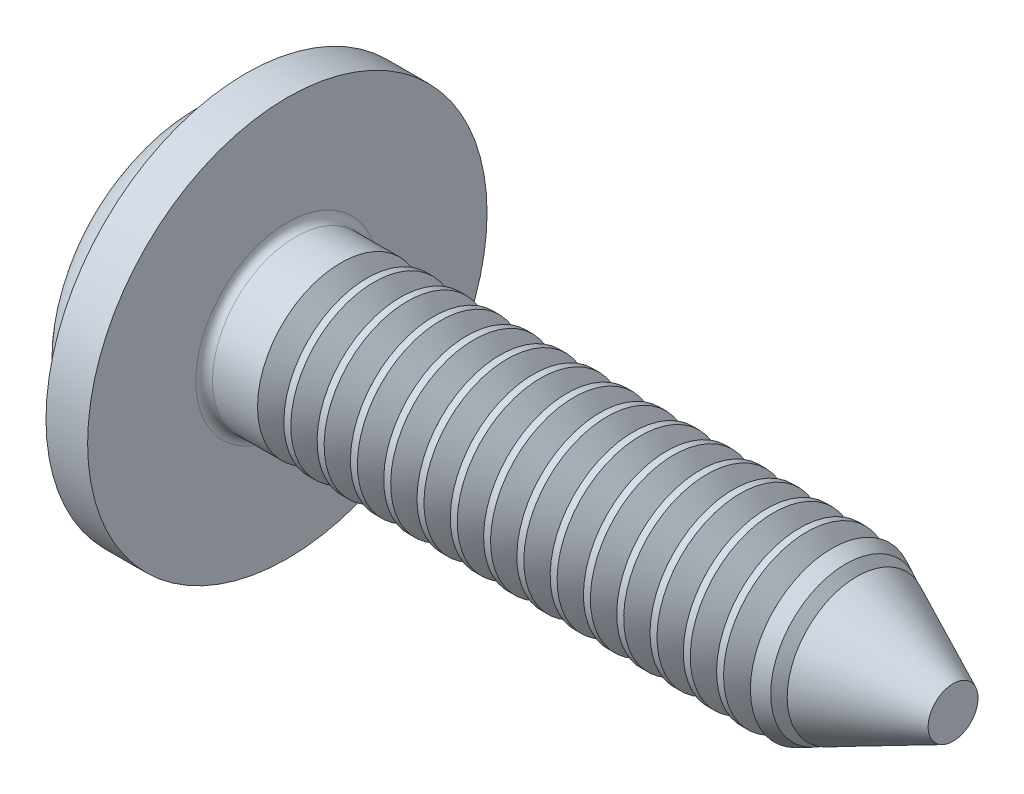
SolidWorks part; units mm, degrees
material "Aço NB 1045"
ref_plane "Plane1" through (0, 0, 0) normal (0, 0, 1) x (1, 0, 0)
ref_plane "Plane2" through (0, 0, 0) normal (0, 1, 0) x (1, 0, 0)
ref_plane "Plane3" through (0, 0, 0) normal (1, 0, 0) x (0, 0, -1)
sketch "BodySke" plane through (0, 0, 0) normal (0, 0, 1) x (1, 0, 0)
  line L0 (1.6, 1) -> (1.6, 2)
  line L1 (1.8, 6.35) -> (1.8, -3.175) construction
  line L2 (-25.4, 0) -> (127, 0) construction
  line L3 (9.6, 0) -> (0, 0)
  line L4 (1.6, 1) -> (9.6, 1)
  line L5 (9.6, 1) -> (9.6, 0)
  line L6 (1.1, 2) -> (1.6, 2)
  line L8 (1.6, 6.35) -> (1.6, -3.175) construction
  arc A0 (0.3941, 1.5765) -> (0, 0) centre (3.35, 0) ccw
  arc A2 (0.3941, 1.5765) -> (1.1, 2) centre (1.1, 1.2) cw
  dimension "D2" = 0.8
  dimension "Length" = 8
  dimension "Head_ht" = 1.6
  dimension "Head_dia" = 4
  dimension "Advance" = 0.4
  dimension "Thread_nom" = 8
  dimension "Diameter" = 2
  dimension "D1" = 0.5
revolve "Base-Revolve" add sketch "BodySke"
cosmetic thread "ThreadCosmetic" [suppressed]
fillet "Fillet1" radius 0.1 1 edges at (1.6, 0, 1)
sketch "Sketch3" plane through (0, 0, 0) normal (1, 0, 0) x (0, 0, -1)
  line L0 (0.24, -1.05) -> (-0.24, -1.05)
  line L1 (0.24, -1.05) -> (0.24, 1.05)
  line L2 (-0.24, 1.05) -> (0.24, 1.05)
  line L3 (-0.24, 1.05) -> (-0.24, -1.05)
  dimension "Cross_dia" = 2.1
  dimension "D1" = 1.05
  dimension "Cross_width" = 0.48
  dimension "D2" = 0.24
ref_plane "Plane4" through (1.42, 0, 0) normal (1, 0, 0) x (0, 0, -1)
sketch "Sketch4" plane through (1.42, 0, 0) normal (1, 0, 0) x (0, 0, -1)
  line L0 (0.24, -0.342) -> (-0.24, -0.342)
  line L1 (0.24, -0.342) -> (0.24, 0.342)
  line L2 (-0.24, 0.342) -> (0.24, 0.342)
  line L3 (-0.24, 0.342) -> (-0.24, -0.342)
  dimension "D1" = 0.48
  dimension "D2" = 0.684
  dimension "D3" = 0.24
  dimension "D4" = 0.342
loft "Recess" cut profiles "Sketch3", "Sketch4"
pattern_circular "RecPat" count 2 every 90 about axis through (0, 0, 0) along (1, 0, 0) of "Recess"
sketch "RecCorSke" plane through (0, 0, 0) normal (0, 0, 1) x (1, 0, 0)
  line L0 (-3.175, 0) -> (15.875, 0) construction
  line L1 (-25.4, 0) -> (127, 0) construction
  line L2 (0, 0) -> (0, 0.4548)
  line L3 (0, 0.4548) -> (1.42, 0.3555)
  line L4 (1.42, 0.3555) -> (1.5355, 0)
  line L5 (1.5355, 0) -> (0, 0)
  dimension "Diameter" = 0.711
  dimension "Depth" = 1.42
  dimension "Draft_angle" = 4
  dimension "Bottom_angle" = 18
revolve "RecessCore" cut sketch "RecCorSke" angle 360 about L0
sketch "ThdSchSke" plane through (0, 0, 0) normal (0, 0, 1) x (1, 0, 0)
  line L0 (2.4, -0.774) -> (2.2418, -1)
  line L1 (2.4, -0.774) -> (2.5582, -1)
  line L2 (2.5582, -1) -> (2.5582, -1.25)
  line L3 (-3.175, 0) -> (5.1513, 0) construction
  line L5 (2.5582, -1.25) -> (2.2418, -1.25)
  line L6 (2.2418, -1.25) -> (2.2418, -1)
  dimension "Diameter" = 2
  dimension "SideAngle" = 55
  dimension "VeeAngle" = 70
  dimension "Thread_minor" = 1.548
  dimension "Overcut" = 2.5
  dimension "Start" = 2.4
revolve "ThreadSchematic" cut sketch "ThdSchSke" angle 360 about L3
pattern_linear "ThdSchPat" count 19 spacing 0.4 along (1, 0, 0) of "ThreadSchematic"
sketch "Esboço1" plane through (1.6, 0, 0) normal (1, 0, 0) x (0, 0, -1)
  circle A0 centre (0, 0) radius 2.4
  dimension "D1" = 4.8
extrude "Ressalto-extrusão1" add sketch "Esboço1" against normal blind 0.5
sketch "Esboço2" plane through (0, 0, 0) normal (0, 1, 0) x (1, 0, 0)
  line L0 (0, 0) -> (9.6, 0) construction
  line L1 (9.6, -0.774) -> (9.6, 0.774) construction
  line L2 (9.6, 0.3) -> (8.1, 1)
  line L4 (8.1, 1) -> (9.6, 1)
  line L5 (9.6, 1) -> (9.6, 0.3)
  line L6 (7.4418, 1) -> (7.3582, 1) construction
  dimension "D1" = 1.5
  dimension "D2" = 0.6
revolve "Corte-Revolução1" cut sketch "Esboço2" angle 360 about L0
equation "\"D1@Sketch3\" = \"Cross_dia@Sketch3\" / 2"
equation "\"D2@Sketch3\" = \"Cross_width@Sketch3\" / 2"
equation "\"Depth@RecCorSke\" = \"Cross_depth@Plane4\""
equation "\"D1@Sketch4\" = \"Cross_width@Sketch3\""
equation "\"D2@Sketch4\" = \"Cross_dia@Sketch3\" - 2.0 * \"Cross_depth@Plane4\" * tan(26.5  * 0.017453292)"
equation "\"D3@Sketch4\" = \"D1@Sketch4\" / 2"
equation "\"D4@Sketch4\" = \"D2@Sketch4\" / 2"
equation "\"Thread_length@ThreadCosmetic\" = ((sgn( (\"Length@BodySke\" - \"Advance@BodySke\" * 2.0 ) - \"Thread_nom@BodySke\" )-1)*( (\"Length@BodySke\" - \"Advance@BodySke\" * 2.0 ) - \"Thread_nom@BodySke\" ))/-2+ \"Thread_nom@BodySke\""
equation "\"Thread_minor@ThdSchSke\" = \"Thread_minor@ThreadCosmetic\""
equation "\"Diameter@ThdSchSke\" = \"Diameter@BodySke\""
equation "\"Overcut@ThdSchSke\" = \"Diameter@BodySke\" * 1.25"
equation "\"Start@ThdSchSke\" = \"Head_ht@BodySke\" + \"Length@BodySke\" - \"Thread_length@ThreadCosmetic\"  '---Non-countersunk---"
equation "\"Num_threads@ThdSchPat\" = int( \"Thread_length@ThreadCosmetic\" / \"Advance@BodySke\" + 0.999 )  + 1"
equation "\"Advance@ThdSchPat\" = \"Thread_length@ThreadCosmetic\" /  (\"Num_threads@ThdSchPat\" - 1) 'relax it"
